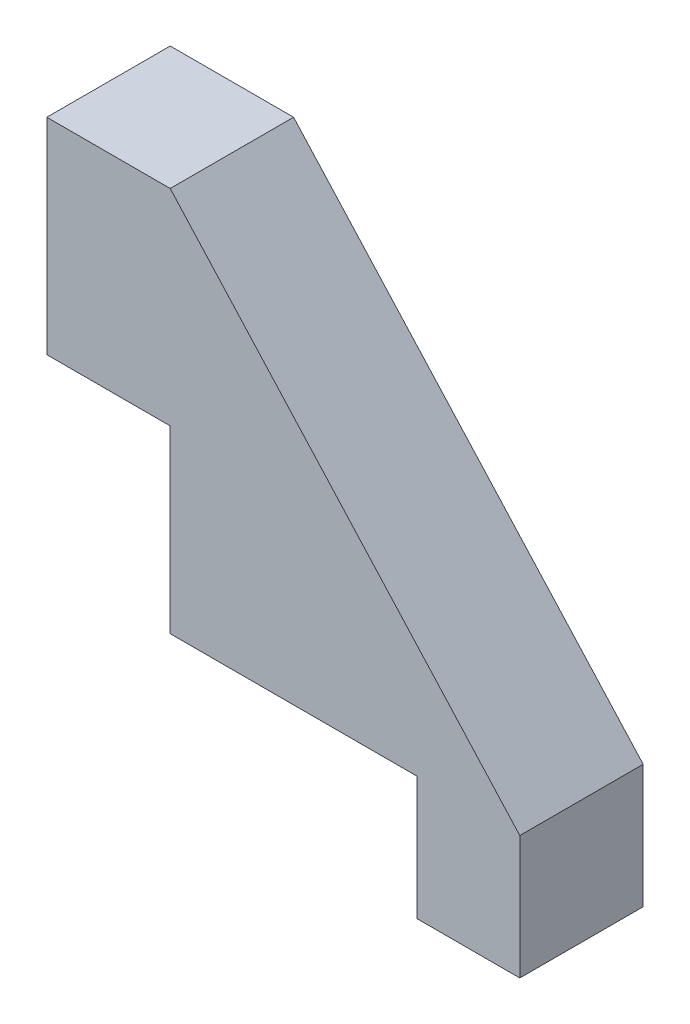
SolidWorks part; units mm, degrees
material "Acrylic (Medium-high impact)"
ref_plane "Front Plane" through (0, 0, 0) normal (0, 0, 1) x (1, 0, 0)
ref_plane "Top Plane" through (0, 0, 0) normal (0, 1, 0) x (1, 0, 0)
ref_plane "Right Plane" through (0, 0, 0) normal (1, 0, 0) x (0, 0, -1)
sketch "Sketch1" plane through (0, 0, 0) normal (0, 0, 1) x (1, 0, 0)
  line L0 (0, 0) -> (0, 8.75)
  line L1 (0, 18.75) -> (17, 0)
  line L2 (12, 0) -> (0, 0)
  line L4 (0, 18.75) -> (-6, 18.75)
  line L6 (0, 8.75) -> (-6, 8.75)
  line L7 (-6, 18.75) -> (-6, 8.75)
  line L9 (17, 0) -> (17, -6)
  line L10 (17, -6) -> (12, -6)
  line L11 (12, 0) -> (12, -6)
  dimension "D1" = 23
  dimension "D2" = 10
  dimension "D3" = 24.75
  dimension "D4" = 6
  dimension "D5" = 5
  dimension "D6" = 6
extrude "Boss-Extrude1" add sketch "Sketch1" along normal blind 6
